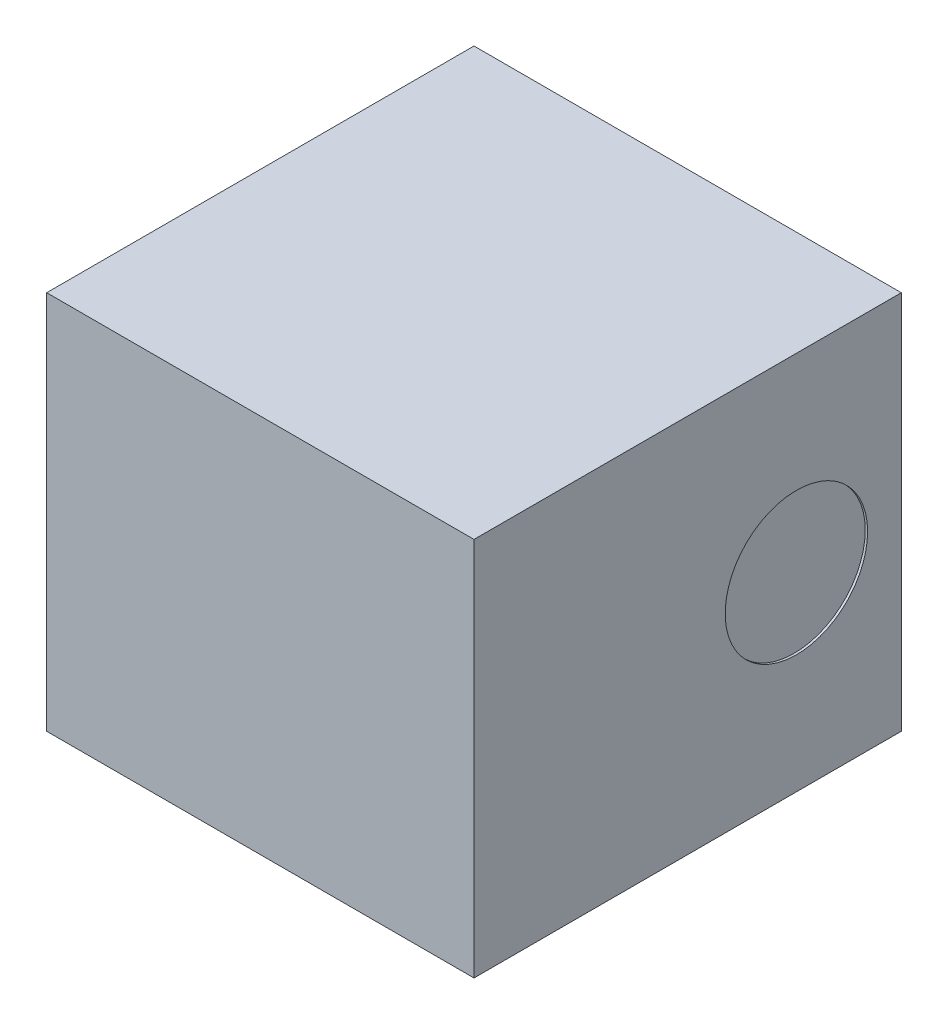
SolidWorks part; units mm, degrees
ref_plane "Front Plane" through (0, 0, 0) normal (0, 0, 1) x (1, 0, 0)
ref_plane "Top Plane" through (0, 0, 0) normal (0, 1, 0) x (1, 0, 0)
ref_plane "Right Plane" through (0, 0, 0) normal (1, 0, 0) x (0, 0, -1)
sketch "Sketch1" plane through (0, 0, 0) normal (0, 1, 0) x (1, 0, 0)
  line L0 (0, 0) -> (18.6879, 0) construction
  line L1 (0, 0) -> (0, -14.4281) construction
  line L3 (-0.45, 0.45) -> (0.45, 0.45)
  line L4 (-0.45, 0.45) -> (-0.45, -0.45)
  line L5 (-0.45, -0.45) -> (0.45, -0.45)
  line L6 (0.45, 0.45) -> (0.45, -0.45)
  dimension "D1" = 0.9
extrude "Boss-Extrude1" add sketch "Sketch1" along normal blind 0.8
ref_plane "Plane1" through (0.45, 0, 0) normal (1, 0, 0) x (0, 0, -1)
sketch "Sketch2" plane through (0.45, 0, 0) normal (1, 0, 0) x (0, 0, -1)
  line L0 (-0.45, 0.4) -> (0.45, 0.4) construction
  line L1 (-0.45, 0.8) -> (-0.45, 0) construction
  line L2 (0.45, 0.8) -> (0.45, 0) construction
  circle A0 centre (0.229, 0.4) radius 0.15
extrude "Cut-Extrude1" cut sketch "Sketch2" against normal blind 0.005 contours A0
